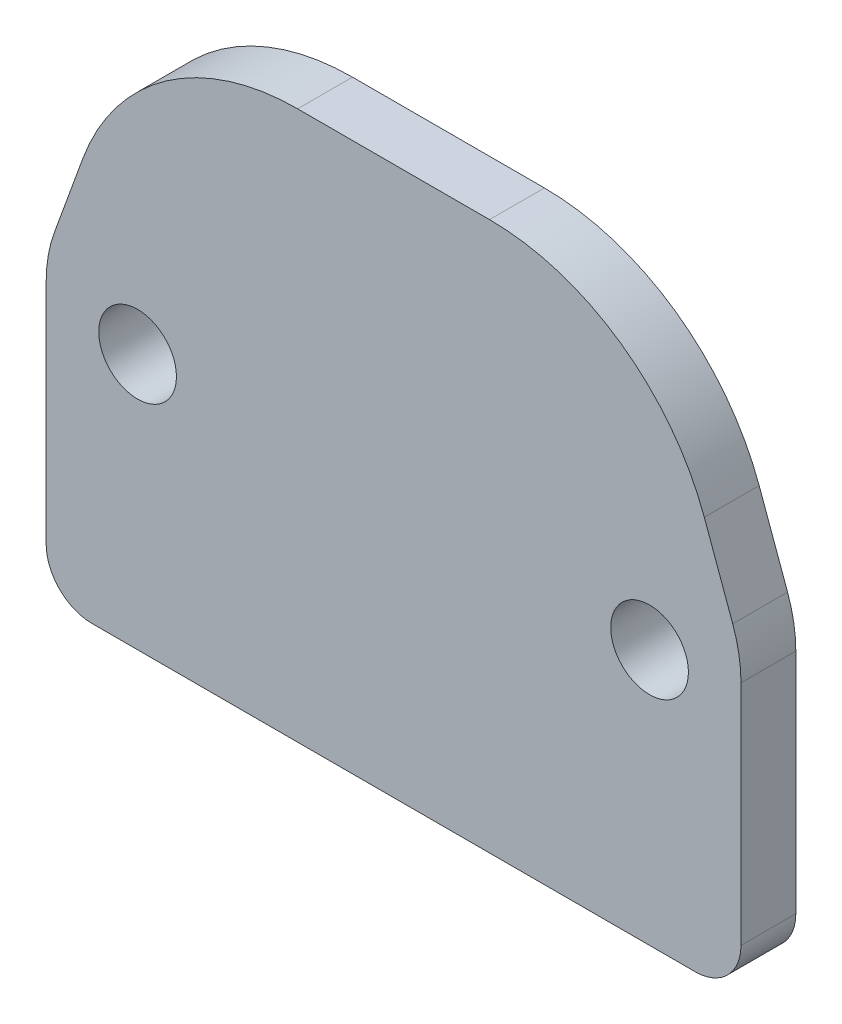
SolidWorks part; units mm, degrees
ref_plane "Plane1" through (0, 0, 0) normal (0, 0, 1) x (1, 0, 0)
ref_plane "Plane2" through (0, 0, 0) normal (0, 1, 0) x (1, 0, 0)
ref_plane "Plane3" through (0, 0, 0) normal (1, 0, 0) x (0, 0, -1)
sketch "Sketch1" plane through (0, 0, 0) normal (0, 0, 1) x (1, 0, 0)
  line L0 (0, -65) -> (0, 0) construction
  line L20 (38, -55) -> (38, -30.1197)
  line L21 (37.0954, -24.9894) -> (33.9871, -16.4495)
  line L22 (10.4948, 0) -> (-10.4948, 0)
  line L23 (-33.9871, -16.4495) -> (-37.0954, -24.9894)
  line L24 (-38, -30.1197) -> (-38, -55)
  line L25 (-33, -60) -> (33, -60)
  circle A2 centre (28, -32) radius 4.25 construction
  circle A3 centre (-28, -32) radius 4.25 construction
  circle A4 centre (-28, -32) radius 4.25
  circle A5 centre (28, -32) radius 4.25
  arc A20 (33, -60) -> (38, -55) centre (33, -55) ccw
  arc A21 (38, -30.1197) -> (37.0954, -24.9894) centre (23, -30.1197) ccw
  arc A22 (33.9871, -16.4495) -> (10.4948, 0) centre (10.4948, -25) ccw
  arc A23 (-10.4948, 0) -> (-33.9871, -16.4495) centre (-10.4948, -25) ccw
  arc A24 (-37.0954, -24.9894) -> (-38, -30.1197) centre (-23, -30.1197) ccw
  arc A25 (-38, -55) -> (-33, -60) centre (-33, -55) ccw
  point P1 (-28, 0)
  point P2 (28, 0)
  point P37 (0, -60)
  dimension "D2" = 8.5
  dimension "D7" = 25
  dimension "D8" = 5
  dimension "D9" = 15
  dimension "D3" = 56
  dimension "D4" = 28
  dimension "D1" = 60
  dimension "D5" = 76
  dimension "D6" = 20
  dimension "D10" = 10
extrude "Extrude1" add sketch "Sketch1" along normal blind 6 separate body
